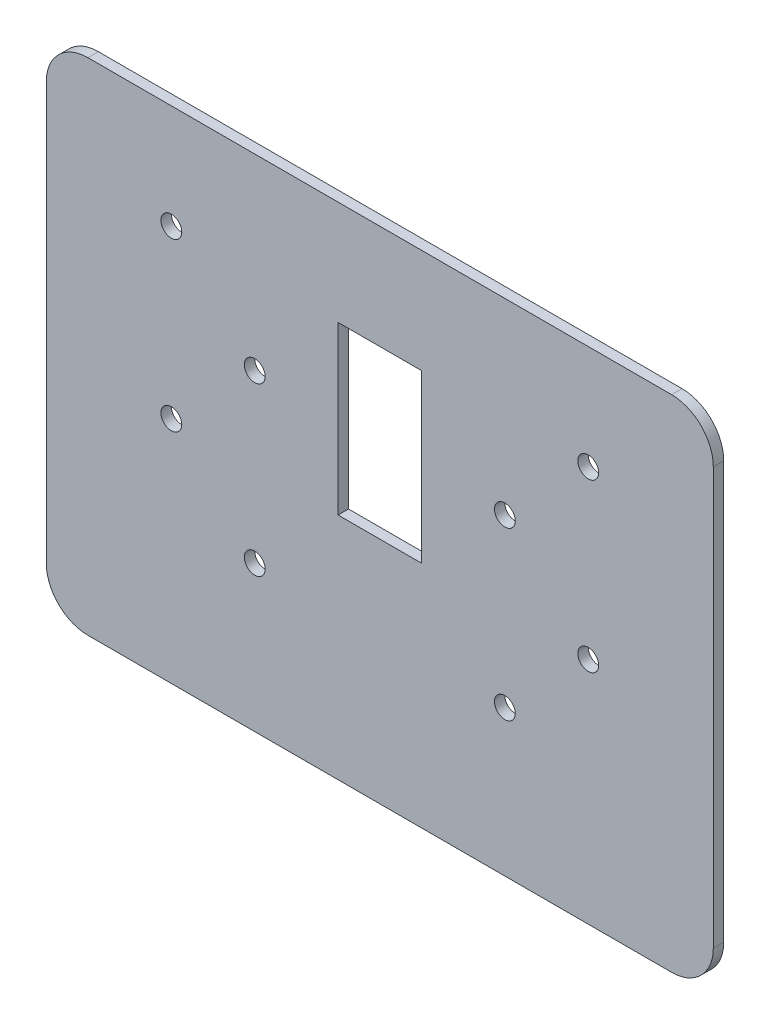
SolidWorks part; units mm, degrees
ref_plane "Front Plane" through (0, 0, 0) normal (0, 0, 1) x (1, 0, 0)
ref_plane "Top Plane" through (0, 0, 0) normal (0, 1, 0) x (1, 0, 0)
ref_plane "Right Plane" through (0, 0, 0) normal (1, 0, 0) x (0, 0, -1)
sketch "Sketch1" plane through (0, 0, 0) normal (0, 0, 1) x (1, 0, 0)
  line L0 (-324.9617, 456.962) -> (-248.7687, 457.9924) construction
  line L1 (-315.8194, 431.7708) -> (-290.4194, 431.7708) construction
  line L2 (-290.4194, 431.7708) -> (-290.4194, 380.9708) construction
  line L3 (-290.4194, 380.9708) -> (-315.8194, 380.9708) construction
  line L4 (-315.8194, 380.9708) -> (-315.8194, 431.7708) construction
  line L5 (-324.9617, 456.962) -> (-248.7687, 457.9924) construction
  line L6 (-315.8194, 431.7708) -> (-290.4194, 431.7708)
  line L7 (-290.4194, 431.7708) -> (-290.4194, 380.9708)
  line L8 (-290.4194, 380.9708) -> (-315.8194, 380.9708)
  line L9 (-315.8194, 380.9708) -> (-315.8194, 431.7708)
  line L10 (-324.9617, 456.962) -> (-458.147, 455.1608) construction
  line L11 (-303.1194, 463.5208) -> (-303.1194, 311.1208) construction
  line L12 (-392.0194, 463.5208) -> (-214.2194, 463.5208)
  line L13 (-404.7194, 450.8208) -> (-404.7194, 323.8208)
  line L14 (-392.0194, 311.1208) -> (-214.2194, 311.1208)
  line L15 (-201.5194, 450.8208) -> (-201.5194, 323.8208)
  line L16 (-404.7194, 387.3208) -> (-201.5194, 387.3208) construction
  circle A0 centre (-239.6194, 431.7708) radius 3.175 construction
  circle A1 centre (-239.6194, 380.9708) radius 3.175 construction
  circle A2 centre (-265.0194, 406.3708) radius 3.175 construction
  circle A3 centre (-366.6194, 380.9708) radius 3.175 construction
  circle A4 centre (-341.2194, 406.3708) radius 3.175 construction
  circle A5 centre (-366.6194, 431.7708) radius 3.175 construction
  circle A6 centre (-239.6194, 431.7708) radius 3.175
  circle A7 centre (-239.6194, 380.9708) radius 3.175
  circle A8 centre (-265.0194, 406.3708) radius 3.175
  circle A9 centre (-366.6194, 380.9708) radius 3.175
  circle A10 centre (-341.2194, 406.3708) radius 3.175
  circle A11 centre (-366.6194, 431.7708) radius 3.175
  arc A12 (-404.7194, 323.8208) -> (-392.0194, 311.1208) centre (-392.0194, 323.8208) ccw
  arc A13 (-214.2194, 311.1208) -> (-201.5194, 323.8208) centre (-214.2194, 323.8208) ccw
  arc A14 (-214.2194, 463.5208) -> (-201.5194, 450.8208) centre (-214.2194, 450.8208) cw
  arc A15 (-392.0194, 463.5208) -> (-404.7194, 450.8208) centre (-392.0194, 450.8208) ccw
  circle A16 centre (-265.0194, 355.5708) radius 3.175 construction
  circle A17 centre (-341.2194, 355.5708) radius 3.175 construction
  circle A18 centre (-265.0194, 355.5708) radius 3.175
  circle A19 centre (-341.2194, 355.5708) radius 3.175
  point P31 (-303.1194, 431.7708)
  point P36 (-404.7194, 311.1208)
  point P41 (-201.5194, 463.5208)
  point P44 (-404.7194, 463.5208)
  dimension "D3" = 12.7
  dimension "D1" = 152.4
  dimension "D2" = 203.2
  dimension "D4" = 31.75
extrude "Boss-Extrude1" add sketch "Sketch1" along normal blind 3.175 contours L12 A15 L13 A12 L14 A13 L15 A14 L8 L9 L6 L7 A6 A7 A8 A9 A10 A11
